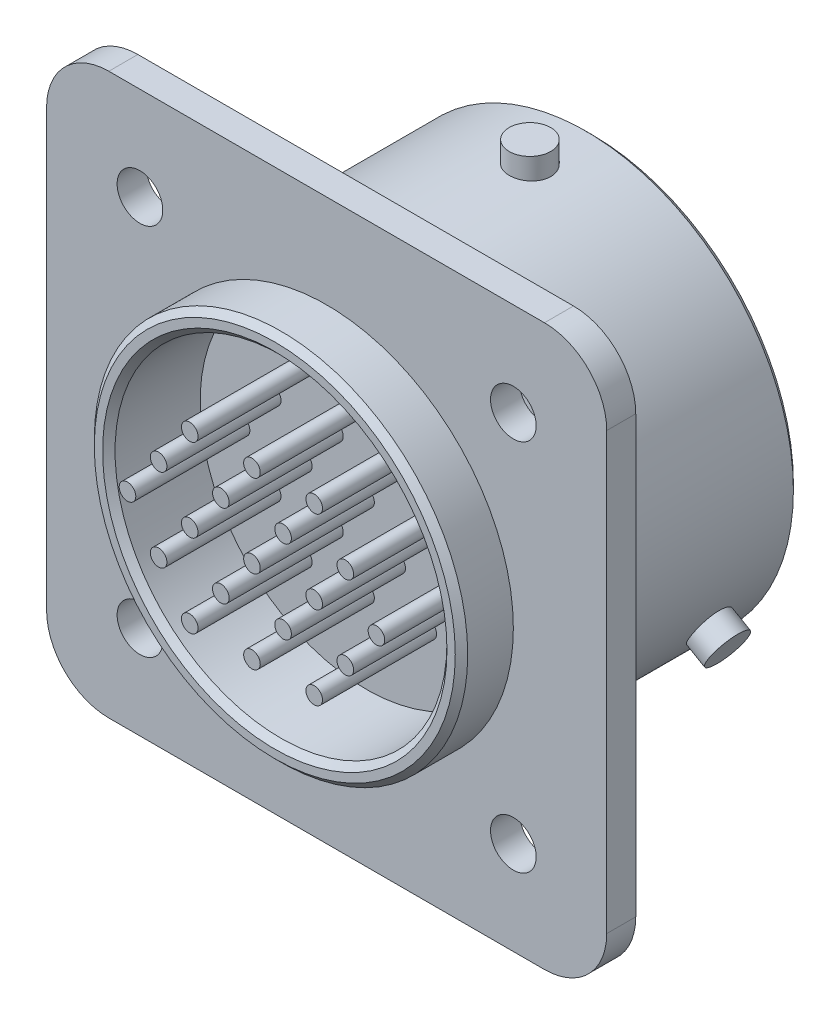
SolidWorks part; units mm, degrees
ref_plane "Спереди" through (0, 0, 0) normal (0, 0, 1) x (1, 0, 0)
ref_plane "Сверху" through (0, 0, 0) normal (0, 1, 0) x (1, 0, 0)
ref_plane "Справа" through (0, 0, 0) normal (1, 0, 0) x (0, 0, -1)
sketch "Эскиз1" plane through (0, 0, 0) normal (0, 0, 1) x (1, 0, 0)
  circle A0 centre (0, 0) radius 9
  dimension "D1" = 18
extrude "Бобышка-Вытянуть1" add sketch "Эскиз1" along normal blind 2.5
sketch "Эскиз2" plane through (0, 0, 0) normal (0, 0, -1) x (-1, 0, 0)
  line L1 (10.5, -13.5) -> (-10.5, -13.5)
  line L2 (13.5, -10.5) -> (13.5, 10.5)
  line L3 (10.5, 13.5) -> (-10.5, 13.5)
  line L4 (-13.5, -10.5) -> (-13.5, 10.5)
  line L5 (13.5, -13.5) -> (-13.5, 13.5) construction
  line L6 (13.5, 13.5) -> (-13.5, -13.5) construction
  arc A0 (-10.5, -13.5) -> (-13.5, -10.5) centre (-10.5, -10.5) cw
  arc A1 (10.5, -13.5) -> (13.5, -10.5) centre (10.5, -10.5) ccw
  arc A2 (13.5, 10.5) -> (10.5, 13.5) centre (10.5, 10.5) ccw
  arc A3 (-10.5, 13.5) -> (-13.5, 10.5) centre (-10.5, 10.5) ccw
  circle A4 centre (9, 9) radius 1.1
  circle A5 centre (-9, 9) radius 1.1
  circle A6 centre (9, -9) radius 1.1
  circle A7 centre (-9, -9) radius 1.1
  point P0 (0, 0)
  dimension "D3" = 3
  dimension "D4" = 2.2
  dimension "D1" = 27
  dimension "D2" = 27
  dimension "D5" = 18
extrude "Бобышка-Вытянуть2" add sketch "Эскиз2" along normal blind 1.4
sketch "Эскиз3" plane through (0, 0, -1.4) normal (0, 0, -1) x (-1, 0, 0)
  circle A0 centre (0, 0) radius 10
  dimension "D1" = 20
extrude "Бобышка-Вытянуть3" add sketch "Эскиз3" along normal blind 11.4
sketch "Эскиз4" plane through (0, 0, 2.5) normal (0, 0, 1) x (1, 0, 0)
  circle A0 centre (0, 0) radius 8
  dimension "D1" = 16
extrude "Вырез-Вытянуть1" cut sketch "Эскиз4" against normal blind 4.4
sketch "Эскиз5" plane through (0, 0, -12.8) normal (0, 0, -1) x (-1, 0, 0)
  circle A0 centre (0, 0) radius 9
  dimension "D1" = 18
extrude "Вырез-Вытянуть2" cut sketch "Эскиз5" against normal blind 7.4
sketch "Эскиз6" plane through (0, 0, -5.4) normal (0, 0, -1) x (-1, 0, 0)
  circle A0 centre (0, 0) radius 8
  dimension "D1" = 16
extrude "Бобышка-Вытянуть4" add sketch "Эскиз6" along normal blind 1
sketch "Эскиз7" plane through (0, 0, -6.4) normal (0, 0, -1) x (-1, 0, 0)
  line L0 (-6, 0) -> (0, 0) construction
  line L1 (0, 0) -> (6, 0) construction
  line L2 (-3, 0) -> (0, 0) construction
  line L3 (-4.5, 2) -> (-1.5, 2) construction
  circle A0 centre (0, 0) radius 0.4
  circle A1 centre (3, 0) radius 0.4
  circle A2 centre (6, 0) radius 0.4
  circle A3 centre (4.5, 2) radius 0.4
  circle A4 centre (-3, 0) radius 0.4
  circle A5 centre (-6, 0) radius 0.4
  circle A6 centre (-4.5, 2) radius 0.4
  circle A7 centre (-1.5, 2) radius 0.4
  circle A8 centre (1.5, 2) radius 0.4
  circle A9 centre (-3, 4) radius 0.4
  circle A10 centre (3, 4) radius 0.4
  circle A11 centre (0, 4) radius 0.4
  circle A12 centre (0, -4) radius 0.4
  circle A13 centre (3, -4) radius 0.4
  circle A14 centre (-3, -4) radius 0.4
  circle A15 centre (1.5, -2) radius 0.4
  circle A16 centre (-1.5, -2) radius 0.4
  circle A17 centre (-4.5, -2) radius 0.4
  circle A18 centre (4.5, -2) radius 0.4
  point P19 (-1.5, 0)
  dimension "D1" = 0.8
  dimension "D4" = 3
  dimension "D5" = 3
  dimension "D2" = 6
  dimension "D3" = 3
  dimension "D6" = 2
  dimension "D7" = 2
extrude "Бобышка-Вытянуть5" add sketch "Эскиз7" along normal blind 5.5 and the other way blind 10
chamfer "Фаска1" distance 0.3 angle 45 4 edges at (-9, 0, -12.8) (-10, 0, -12.8) (8, 0, 2.5) (9, 0, 2.5)
sketch "Эскиз8" plane through (0, 0, 0) normal (0, 1, 0) x (1, 0, 0)
  line L0 (9.7, 12.8) -> (-9.7, 12.8) construction
  circle A0 centre (0, 9.8) radius 1
  dimension "D2" = 2
  dimension "D1" = 3
extrude "Бобышка-Вытянуть6" add sketch "Эскиз8" along normal blind 1 and the other way up to body from offset 10 separate body
pattern_circular "Круговой массив1" count 3 over 360 about axis through (0, 0, 0) along (0, 0, 1) of "Бобышка-Вытянуть6"
